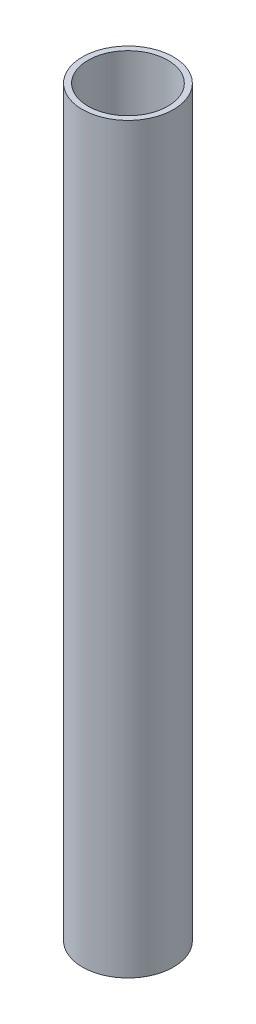
SolidWorks part; units mm, degrees
material "AISI 304"
ref_plane "前视基准面" through (0, 0, 0) normal (0, 0, 1) x (1, 0, 0)
ref_plane "上视基准面" through (0, 0, 0) normal (0, 1, 0) x (1, 0, 0)
ref_plane "右视基准面" through (0, 0, 0) normal (1, 0, 0) x (0, 0, -1)
other "Configuration Table"
sketch "草图1" plane through (0, 0, 0) normal (0, 1, 0) x (1, 0, 0)
  circle A0 centre (0, 0) radius 3.5
  circle A1 centre (0, 0) radius 4
  dimension "D1" = 7
  dimension "D2" = 8
extrude "凸台-拉伸1" add sketch "草图1" along normal blind 65.19
